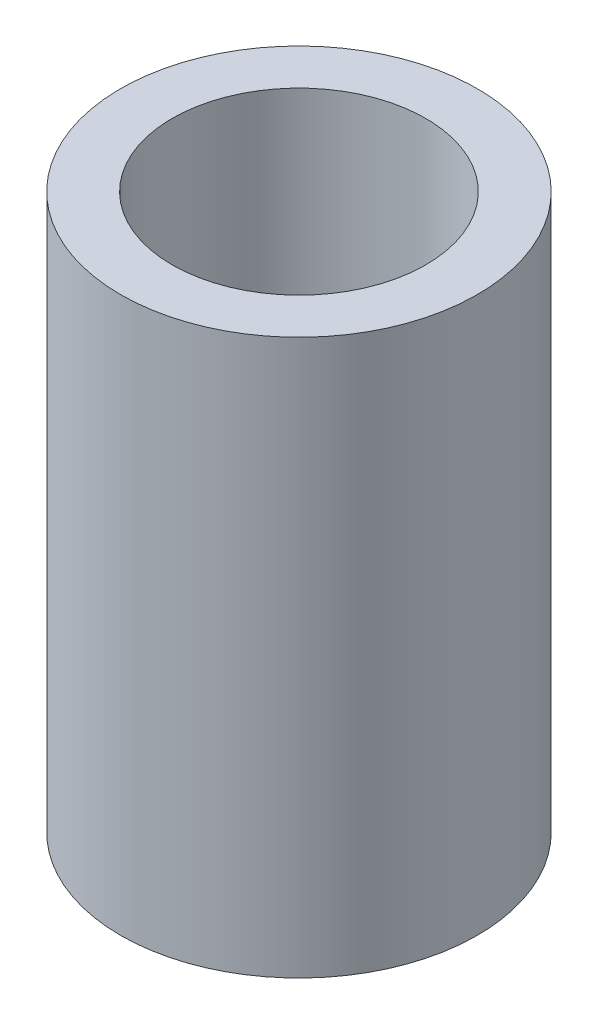
SolidWorks part; units mm, degrees
ref_plane "Front Plane" through (0, 0, 0) normal (0, 0, 1) x (1, 0, 0)
ref_plane "Top Plane" through (0, 0, 0) normal (0, 1, 0) x (1, 0, 0)
ref_plane "Right Plane" through (0, 0, 0) normal (1, 0, 0) x (0, 0, -1)
sketch "Sketch1" plane through (0, 0, 0) normal (0, 1, 0) x (1, 0, 0)
  circle A0 centre (0, 0) radius 6.75
extrude "Boss-Extrude1" add sketch "Sketch1" along normal blind 21
sketch "Sketch2" plane through (0, 21, 0) normal (0, 1, 0) x (1, 0, 0)
  circle A0 centre (0, 0) radius 4.8
  dimension "D1" = 9.6
extrude "Cut-Extrude1" cut sketch "Sketch2" against normal blind 10
sketch "Sketch3" plane through (0, 0, 0) normal (0, -1, 0) x (1, 0, 0)
  line L0 (-1.2975, -1.0984) -> (1.2975, -1.0984)
  line L1 (-1.15, -0.7984) -> (1.15, -0.7984)
  arc A0 (1.15, -0.7984) -> (-1.15, -0.7984) centre (0, 0) ccw
  arc A1 (1.2975, -1.0984) -> (-1.2975, -1.0984) centre (0, 0) ccw
  dimension "D1" = 2.3
  dimension "D2" = 1.4
  dimension "D3" = 0.3
extrude "Cut-Extrude2" cut sketch "Sketch3" against normal blind 9 contours A1 L0
